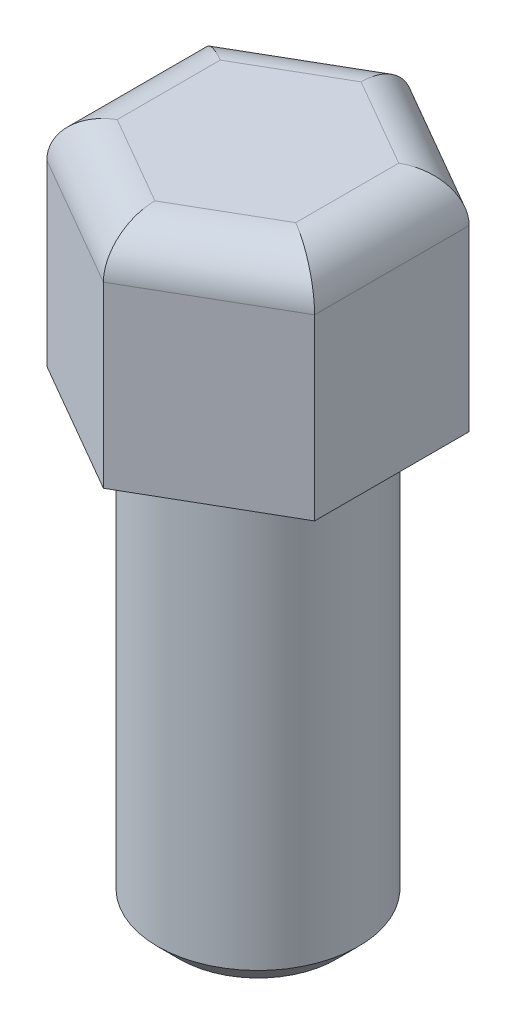
SolidWorks part; units mm, degrees
ref_plane "前基準面" through (0, 0, 0) normal (0, 0, 1) x (1, 0, 0)
ref_plane "上基準面" through (0, 0, 0) normal (0, 1, 0) x (1, 0, 0)
ref_plane "右基準面" through (0, 0, 0) normal (1, 0, 0) x (0, 0, -1)
sketch "草圖1" plane through (0, 0, 0) normal (0, 1, 0) x (1, 0, 0)
  circle A0 centre (0, 0) radius 4.5
  dimension "D1" = 9
extrude "填料-伸長1" add sketch "草圖1" along normal blind 20
sketch "草圖2" plane through (0, 20, 0) normal (0, 1, 0) x (1, 0, 0)
  line L1 (6, 3.4641) -> (0, 6.9282)
  line L2 (0, 6.9282) -> (-6, 3.4641)
  line L3 (-6, 3.4641) -> (-6, -3.4641)
  line L4 (-6, -3.4641) -> (0, -6.9282)
  line L5 (0, -6.9282) -> (6, -3.4641)
  line L6 (6, -3.4641) -> (6, 3.4641)
  circle A0 centre (0, 0) radius 6 construction
  dimension "D1" = 12
extrude "填料-伸長2" add sketch "草圖2" along normal blind 10
chamfer "導角2" distance 1 angle 45 2 edges at (0, 20, 4.5) (0, 0, 4.5)
fillet "圓角1" radius 2 6 edges at (-6, 30, 0) (-3, 30, 5.1962) (3, 30, 5.1962) (6, 30, 0) (3, 30, -5.1962) (-3, 30, -5.1962)
